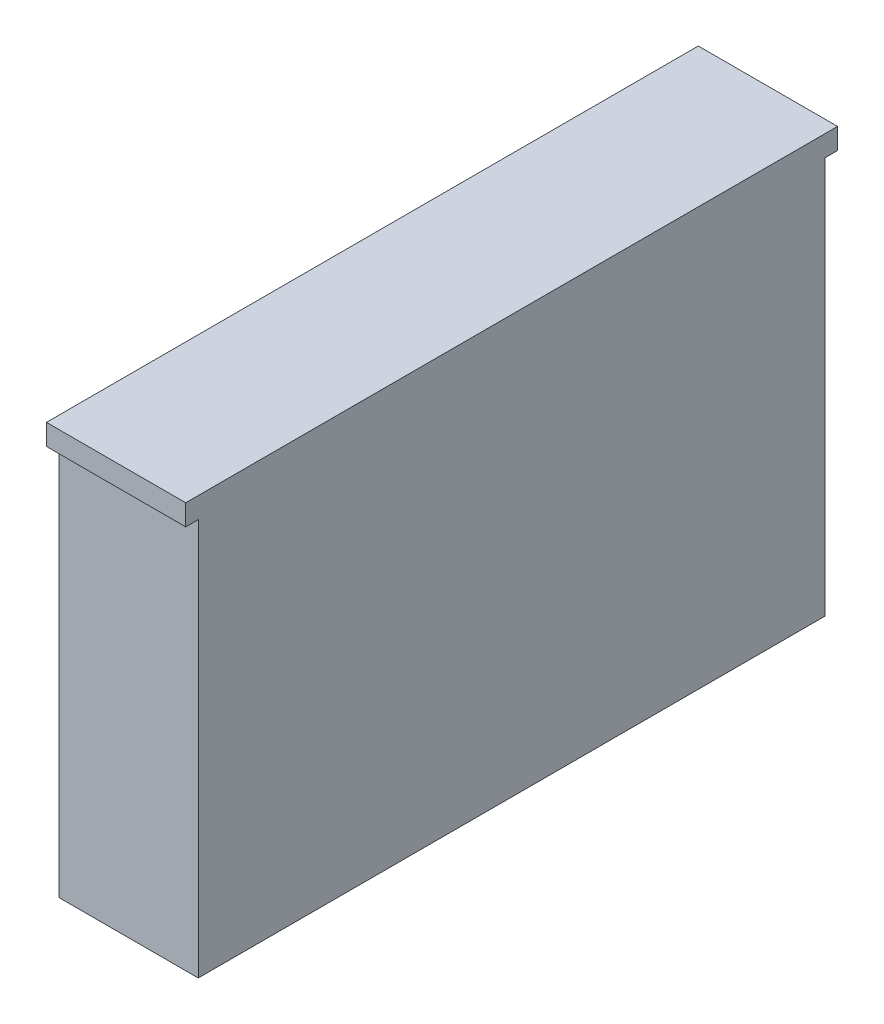
SolidWorks part; units mm, degrees
ref_plane "Alzado" through (0, 0, 0) normal (0, 0, 1) x (1, 0, 0)
ref_plane "Planta" through (0, 0, 0) normal (0, 1, 0) x (1, 0, 0)
ref_plane "Vista lateral" through (0, 0, 0) normal (1, 0, 0) x (0, 0, -1)
sketch "Croquis2" plane through (0, 0, 0) normal (1, 0, 0) x (0, 0, -1)
  line L1 (225, -150) -> (-225, -150)
  line L2 (225, -150) -> (225, 150)
  line L3 (225, 150) -> (-225, 150)
  line L4 (-225, -150) -> (-225, 150)
  line L5 (225, -150) -> (-225, 150) construction
  line L6 (225, 150) -> (-225, -150) construction
  point P0 (0, 0)
  dimension "D1" = 300
  dimension "D2" = 450
extrude "Saliente-Extruir1" add sketch "Croquis2" along normal blind 100
sketch "Croquis3" plane through (0, 0, 0) normal (-1, 0, 0) x (0, 0, 1)
  line L0 (-85.1737, 98.5116) -> (-2.5894, 8.4513) construction
  line L1 (-822.5697, 83.8671) -> (1.4303, 83.8671) construction
sketch "Croquis4" plane through (0, 0, -225) normal (0, 0, -1) x (-1, 0, 0)
  line L0 (-100, 150) -> (0, 150) construction
  line L5 (-100, 150) -> (0, 150)
  line L6 (0, 150) -> (0, 135)
  line L7 (0, -150) -> (0, 150) construction
  line L8 (0, 135) -> (-100, 135)
  line L9 (-100, -150) -> (-100, 150) construction
  line L10 (-100, 135) -> (-100, 150)
  point P0 (-79.3167, 150)
  dimension "D1" = 15
extrude "Saliente-Extruir2" add sketch "Croquis4" along normal blind 9
sketch "Croquis5" plane through (0, 0, 225) normal (0, 0, 1) x (1, 0, 0)
  line L1 (0, 150) -> (100, 150)
  line L2 (100, 150) -> (100, 135)
  line L3 (100, 135) -> (0, 135)
  line L4 (0, 135) -> (0, 150)
extrude "Saliente-Extruir3" add sketch "Croquis5" along normal blind 9
sketch "Croquis6" plane through (0, 0, -225) normal (0, 0, -1) x (-1, 0, 0)
  line L0 (-45.7416, -114.9273) -> (182.2584, -114.9273) construction
sketch "Croquis7" plane through (0, 0, -225) normal (0, 0, -1) x (-1, 0, 0)
  line L0 (-17.8265, -149.264) -> (210.1735, -149.264) construction
  line L1 (-208.937, -73.3363) -> (-75.6037, -73.3363) construction
sketch "Croquis8" plane through (0, -150, 0) normal (0, -1, 0) x (1, 0, 0)
  line L0 (-86.3236, 82.273) -> (47.0097, 82.273) construction
sketch "Croquis9" plane through (0, 0, 0) normal (-1, 0, 0) x (0, 0, 1)
  line L0 (-99.6421, -23.8204) -> (-52.3088, -23.8204) construction
sketch "Croquis10" plane through (0, 0, 0) normal (-1, 0, 0) x (0, 0, 1)
  line L0 (-79.3698, -143.6865) -> (-50.0365, -143.6865) construction
  line L1 (-79.5365, 75.9615) -> (-50.8698, 75.9615) construction
  line L2 (18.9393, -6.6427) -> (68.2726, -6.6427) construction
sketch "Croquis11" plane through (0, 0, 0) normal (-1, 0, 0) x (0, 0, 1)
  line L0 (-24.5347, -157.991) -> (314.132, -157.991) construction
